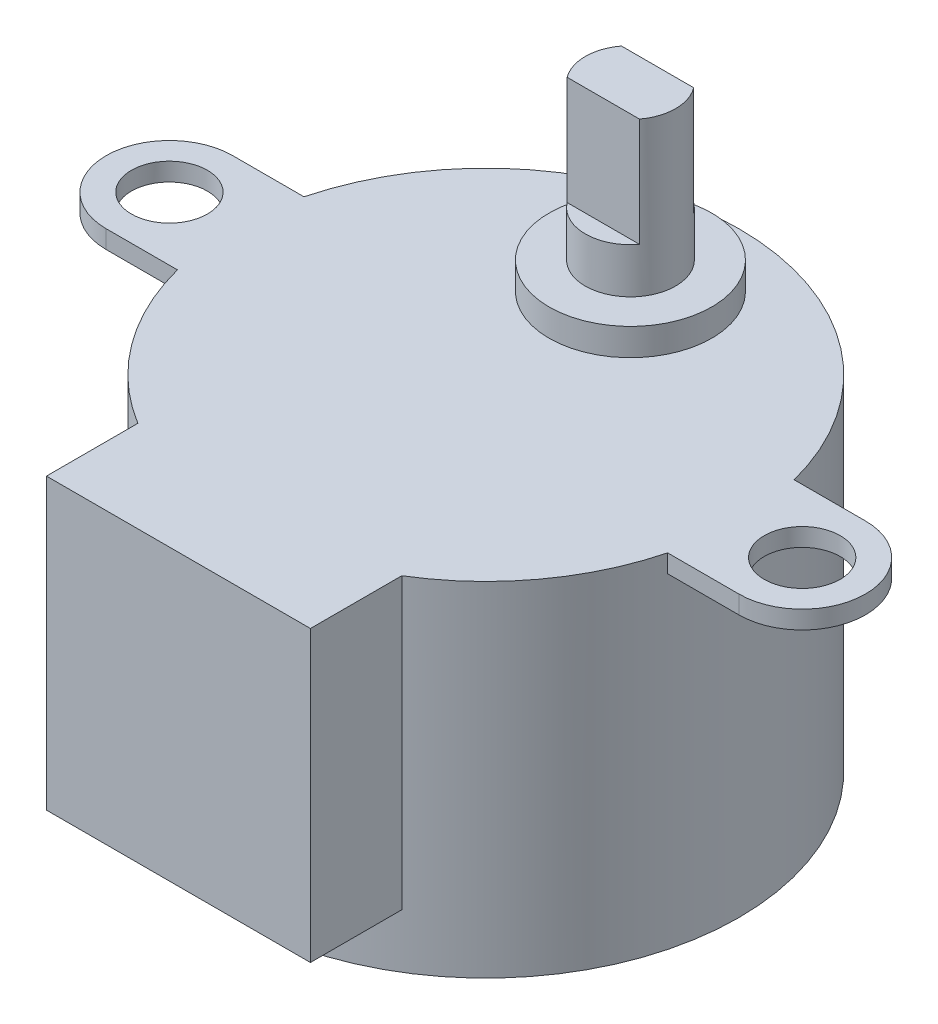
SolidWorks part; units mm, degrees
ref_plane "Front Plane" through (0, 0, 0) normal (0, 0, 1) x (1, 0, 0)
ref_plane "Top Plane" through (0, 0, 0) normal (0, 1, 0) x (1, 0, 0)
ref_plane "Right Plane" through (0, 0, 0) normal (1, 0, 0) x (0, 0, -1)
sketch "Sketch1" plane through (0, 0, 0) normal (0, 1, 0) x (1, 0, 0)
  circle A0 centre (0, 0) radius 14
  dimension "D1" = 28
extrude "Boss-Extrude1" add sketch "Sketch1" along normal blind 19
sketch "Sketch2" plane through (0, 19, 0) normal (0, 1, 0) x (1, 0, 0)
  line L0 (-25.598, 0) -> (28.6857, 0) construction
  line L1 (13.5554, 3.5) -> (17.5, 3.5)
  line L2 (13.5554, -3.5) -> (17.5, -3.5)
  line L3 (0, 23.3673) -> (0, -19.8604) construction
  line L4 (-13.5554, -3.5) -> (-17.5, -3.5)
  line L5 (-13.5554, 3.5) -> (-17.5, 3.5)
  arc A1 (17.5, -3.5) -> (17.5, 3.5) centre (17.5, 0) ccw
  arc A3 (13.5554, -3.5) -> (13.5554, 3.5) centre (0, 0) ccw
  arc A4 (-17.5, -3.5) -> (-17.5, 3.5) centre (-17.5, 0) cw
  arc A5 (-13.5554, -3.5) -> (-13.5554, 3.5) centre (0, 0) cw
  point P3 (17.5, 0)
  point P20 (-17.5, 0)
  dimension "D2" = 3.5
  dimension "D1" = 17.5
extrude "Boss-Extrude2" add sketch "Sketch2" against normal blind 1
sketch "Sketch3" plane through (0, 19, 0) normal (0, 1, 0) x (1, 0, 0)
  circle A0 centre (17.5, 0) radius 2.1
  circle A1 centre (-17.5, 0) radius 2.1
  point P0 (17.5, 0)
  point P1 (-17.5, 0)
  dimension "D3" = 4.2
  dimension "D4" = 4.2
  dimension "D1" = 35
  dimension "D2" = 17.5
extrude "Cut-Extrude1" cut sketch "Sketch3" against normal up to next
sketch "Sketch4" plane through (0, 19, 0) normal (0, 1, 0) x (1, 0, 0)
  line L1 (0, 20.817) -> (0, -22.5887) construction
  line L2 (7.3, -11.9461) -> (7.3, -17)
  line L3 (-7.3, -11.9461) -> (-7.3, -17)
  line L4 (-7.3, -17) -> (7.3, -17)
  line L5 (-7.3, -17) -> (7.3, -17) construction
  arc A0 (-7.3, -11.9461) -> (7.3, -11.9461) centre (0, 0) ccw
  dimension "D2" = 7.3
extrude "Boss-Extrude3" add sketch "Sketch4" against normal blind 16 contours L3 L4 L2 A0
sketch "Sketch5" plane through (0, 19, 0) normal (0, 1, 0) x (1, 0, 0)
  circle A0 centre (0, 8) radius 4.5
  point P0 (0, 8)
  dimension "D2" = 9
  dimension "D1" = 8
extrude "Boss-Extrude4" add sketch "Sketch5" along normal blind 1.5
sketch "Sketch6" plane through (0, 20.5, 0) normal (0, 1, 0) x (1, 0, 0)
  circle A0 centre (0, 8) radius 2.5
  point P0 (0, 8)
  dimension "D1" = 5
extrude "Boss-Extrude5" add sketch "Sketch6" along normal blind 2.5
sketch "Sketch7" plane through (0, 23, 0) normal (0, 1, 0) x (1, 0, 0)
  line L0 (-2, 9.5) -> (2, 9.5)
  line L1 (-2.5, 8) -> (2.5, 8) construction
  line L2 (-2, 6.5) -> (2, 6.5)
  arc A0 (-2, 9.5) -> (-2, 6.5) centre (0, 8) ccw
  arc A1 (2, 6.5) -> (2, 9.5) centre (0, 8) ccw
  point P0 (0, 8)
  dimension "D1" = 8
  dimension "D2" = 1.5
extrude "Boss-Extrude6" add sketch "Sketch7" along normal blind 6
